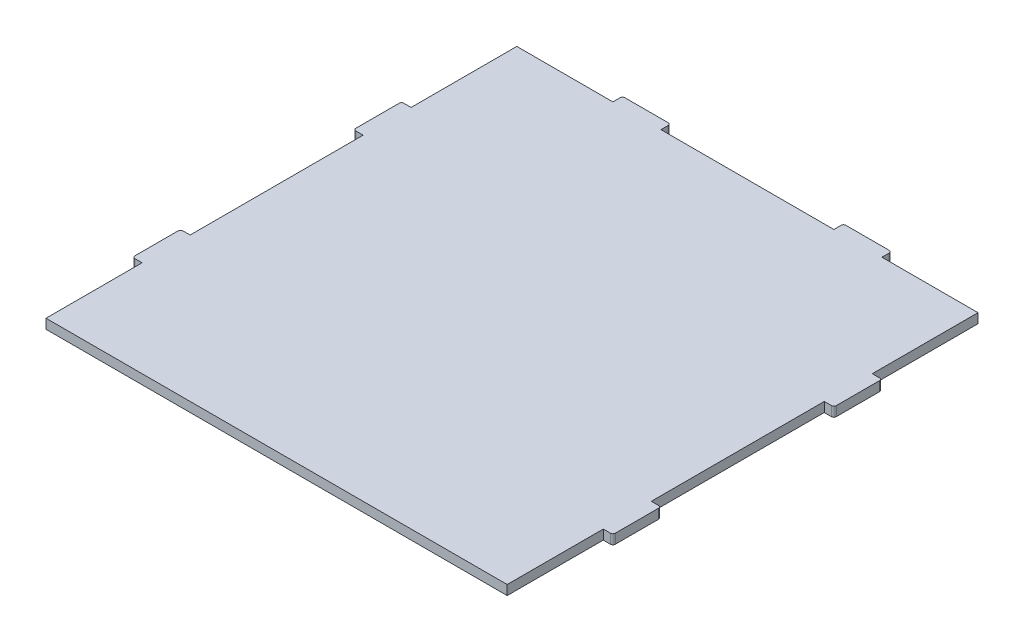
SolidWorks part; units mm, degrees
ref_plane "Front Plane" through (0, 0, 0) normal (0, 0, 1) x (1, 0, 0)
ref_plane "Top Plane" through (0, 0, 0) normal (0, 1, 0) x (1, 0, 0)
ref_plane "Right Plane" through (0, 0, 0) normal (1, 0, 0) x (0, 0, -1)
sketch "Sketch1" plane through (0, 0, 0) normal (0, 0, 1) x (1, 0, 0)
  line L0 (48, 50) -> (48, -50) construction
  line L1 (-48, 50) -> (48, 50)
  line L2 (-48, 50) -> (-48, 48)
  line L3 (-48, 48) -> (48, 48)
  line L4 (48, 50) -> (48, 48)
  dimension "D1" = 2
extrude "Boss-Extrude1" add sketch "Sketch1" along normal up to surface (98 mm away)
sketch "Sketch2" plane through (0, 0, 0) normal (0, 0, -1) x (-1, 0, 0)
  line L0 (-48, 50) -> (48, 50) construction
  line L1 (-28, 50) -> (-18, 50)
  line L2 (-28, 50) -> (-28, 48)
  line L3 (-28, 48) -> (-18, 48)
  line L4 (-18, 50) -> (-18, 48)
  line L5 (48, 48) -> (-48, 48) construction
  line L6 (-48, 48) -> (-48, 50) construction
  dimension "D1" = 30
  dimension "D2" = 20
extrude "Boss-Extrude2" add sketch "Sketch2" along normal up to surface (2 mm away)
mirror "Mirror1" about plane through (0, 0, 0) normal (1, 0, 0) of "Boss-Extrude2"
sketch "Sketch3" plane through (-48, 0, 0) normal (-1, 0, 0) x (0, 0, 1)
  line L0 (98, 50) -> (0, 50) construction
  line L1 (78, 50) -> (68, 50)
  line L2 (78, 50) -> (78, 48)
  line L3 (78, 48) -> (68, 48)
  line L4 (68, 50) -> (68, 48)
  line L5 (98, 48) -> (0, 48) construction
  line L6 (98, 48) -> (98, 50) construction
  point P8 (78, 49)
  dimension "D1" = 20
  dimension "D2" = 30
extrude "Boss-Extrude3" add sketch "Sketch3" along normal up to surface (2 mm away)
ref_plane "Plane1" through (0, 0, 50) normal (0, 0, 1) x (1, 0, 0)
mirror "Mirror2" about plane through (0, 0, 50) normal (0, 0, 1) of "Boss-Extrude3"
sketch "Sketch4" plane through (48, 0, 0) normal (1, 0, 0) x (0, 0, -1)
  line L0 (-98, 48) -> (0, 48) construction
  line L1 (-68, 48) -> (-78, 48)
  line L2 (-68, 48) -> (-68, 50)
  line L3 (-68, 50) -> (-78, 50)
  line L4 (-78, 48) -> (-78, 50)
  line L5 (-98, 50) -> (0, 50) construction
  line L6 (-98, 50) -> (-98, 48) construction
  dimension "D1" = 20
  dimension "D2" = 30
extrude "Boss-Extrude4" add sketch "Sketch4" along normal up to surface (2 mm away)
mirror "Mirror3" about plane through (0, 0, 50) normal (0, 0, 1) of "Boss-Extrude4"
fillet "Fillet1" radius 0.5 12 edges at (-50, 49, 22) (-50, 49, 32) (-50, 49, 68) (-50, 49, 78) (50, 49, 78) (50, 49, 68) (50, 49, 22) (50, 49, 32) (28, 49, -2) (18, 49, -2) (-18, 49, -2) (-28, 49, -2)
